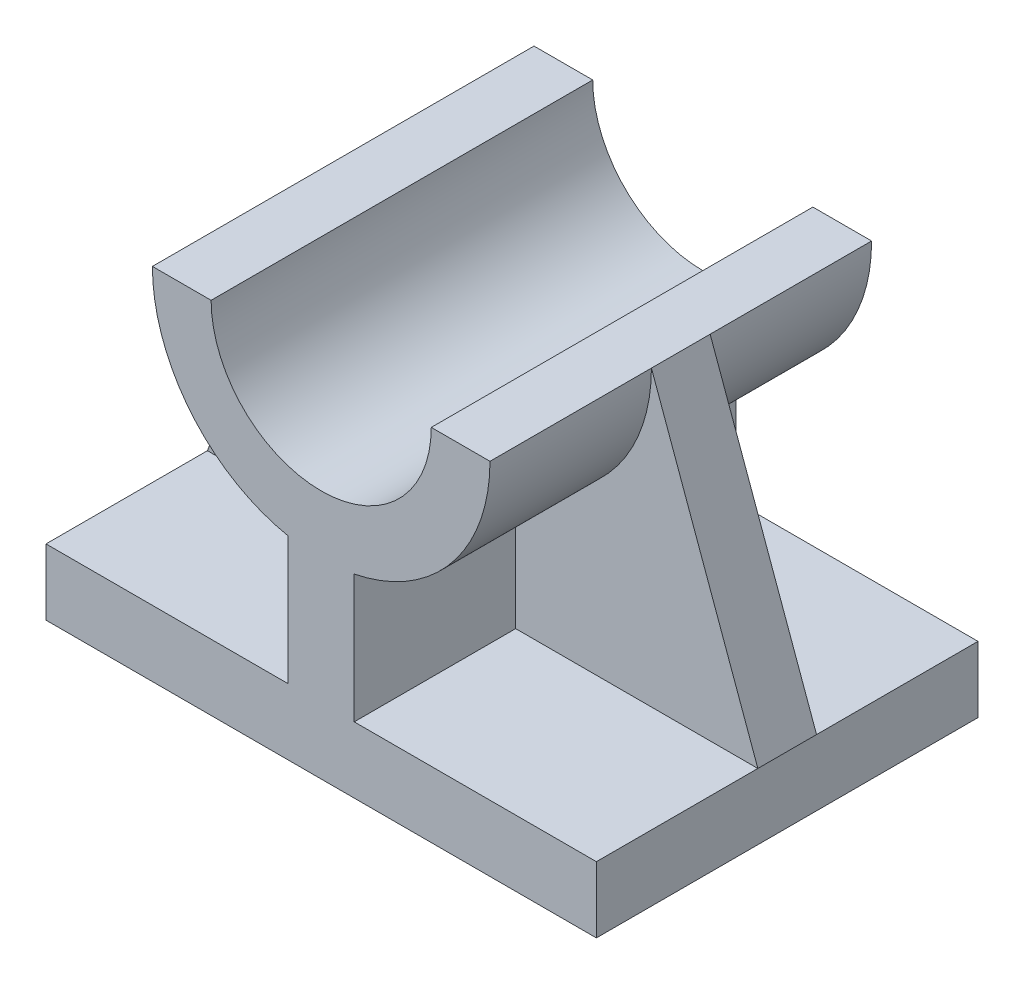
SolidWorks part; units mm, degrees
ref_plane "Front Plane" through (0, 0, 0) normal (0, 0, 1) x (1, 0, 0)
ref_plane "Top Plane" through (0, 0, 0) normal (0, 1, 0) x (1, 0, 0)
ref_plane "Right Plane" through (0, 0, 0) normal (1, 0, 0) x (0, 0, -1)
sketch "Sketch2" plane through (0, 0, 0) normal (0, 0, 1) x (1, 0, 0)
  line L0 (-23, 44.5) -> (-15, 44.5)
  line L1 (-37.5, 4.5) -> (-4.5, 4.5)
  line L2 (-37.5, 4.5) -> (-37.5, -4.5)
  line L3 (-37.5, -4.5) -> (37.5, -4.5)
  line L4 (37.5, 4.5) -> (37.5, -4.5)
  line L5 (-37.5, 4.5) -> (37.5, -4.5) construction
  line L6 (-37.5, -4.5) -> (37.5, 4.5) construction
  line L7 (15, 44.5) -> (23, 44.5)
  line L8 (-4.5, 4.5) -> (-4.5, 21.9445)
  line L9 (0, 4.5) -> (0, 21.5) construction
  line L10 (4.5, 4.5) -> (4.5, 21.9445)
  line L11 (4.5, 4.5) -> (37.5, 4.5)
  arc A0 (-23, 44.5) -> (-4.5, 21.9445) centre (0, 44.5) ccw
  arc A1 (-15, 44.5) -> (15, 44.5) centre (0, 44.5) ccw
  arc A2 (4.5, 21.9445) -> (23, 44.5) centre (0, 44.5) ccw
  point P0 (0, 0)
  dimension "D3" = 46
  dimension "D4" = 30
  dimension "D1" = 75
  dimension "D2" = 9
  dimension "D5" = 40
  dimension "D6" = 4.5
extrude "Boss-Extrude1" add sketch "Sketch2" against normal mid plane 52
sketch "Sketch3" plane through (0, 0, 0) normal (0, 0, 1) x (1, 0, 0)
  line L0 (23, 44.5) -> (37.5, 4.5)
rib "Rib1" sketch "Sketch3" sketch "Sketch3" thickness 8 extrusion direction parallel to sketch draft on no parameters "D1"=8
mirror "Mirror1" about plane through (0, 0, 0) normal (1, 0, 0) of "Rib1"
